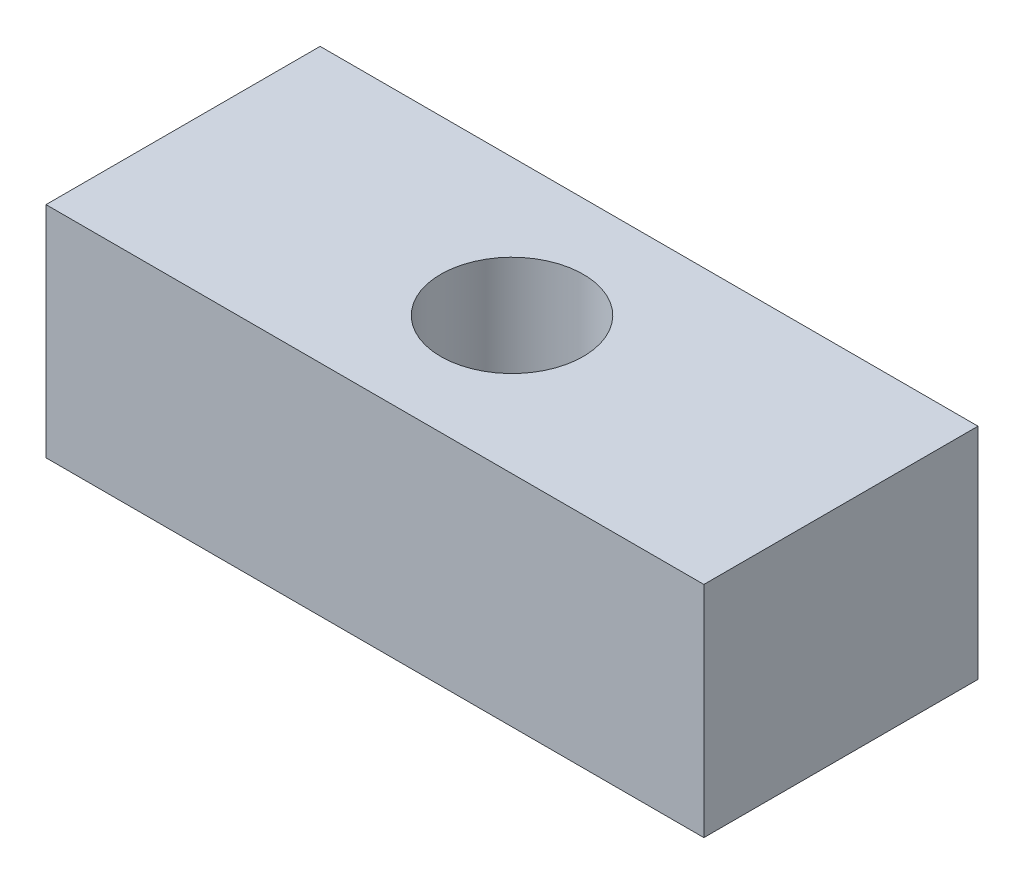
SolidWorks part; units mm, degrees
ref_plane "Alzado" through (0, 0, 0) normal (0, 0, 1) x (1, 0, 0)
ref_plane "Planta" through (0, 0, 0) normal (0, 1, 0) x (1, 0, 0)
ref_plane "Vista lateral" through (0, 0, 0) normal (1, 0, 0) x (0, 0, -1)
sketch "Croquis1" plane through (0, 0, 0) normal (0, 0, 1) x (1, 0, 0)
  line L0 (-30, 10) -> (30, -10) construction
  line L1 (-30, 10) -> (30, 10)
  line L2 (-30, 10) -> (-30, -10)
  line L3 (-30, -10) -> (30, -10)
  line L4 (30, 10) -> (30, -10)
  dimension "D1" = 60
  dimension "D2" = 20
extrude "Saliente-Extruir1" add sketch "Croquis1" along normal blind 25 contours L1 L4 L3 L2
sketch "Croquis2" plane through (0, 10, 0) normal (0, 1, 0) x (1, 0, 0)
  line L0 (-30, 0) -> (30, -25) construction
  line L4 (30, 0) -> (-30, 0)
  line L5 (-30, 0) -> (-30, -25)
  line L6 (-30, -25) -> (30, -25)
  line L7 (30, -25) -> (30, 0)
  line L8 (30, 0) -> (-30, 0) construction
  line L9 (-30, 0) -> (-30, -25) construction
  line L10 (-30, -25) -> (30, -25) construction
  line L11 (30, -25) -> (30, 0) construction
  circle A0 centre (0, -12.5) radius 6.5
  dimension "D2" = 13
  dimension "D1" = 0
extrude "Cortar-Extruir1" cut sketch "Croquis2" against normal blind 20 contours A0
